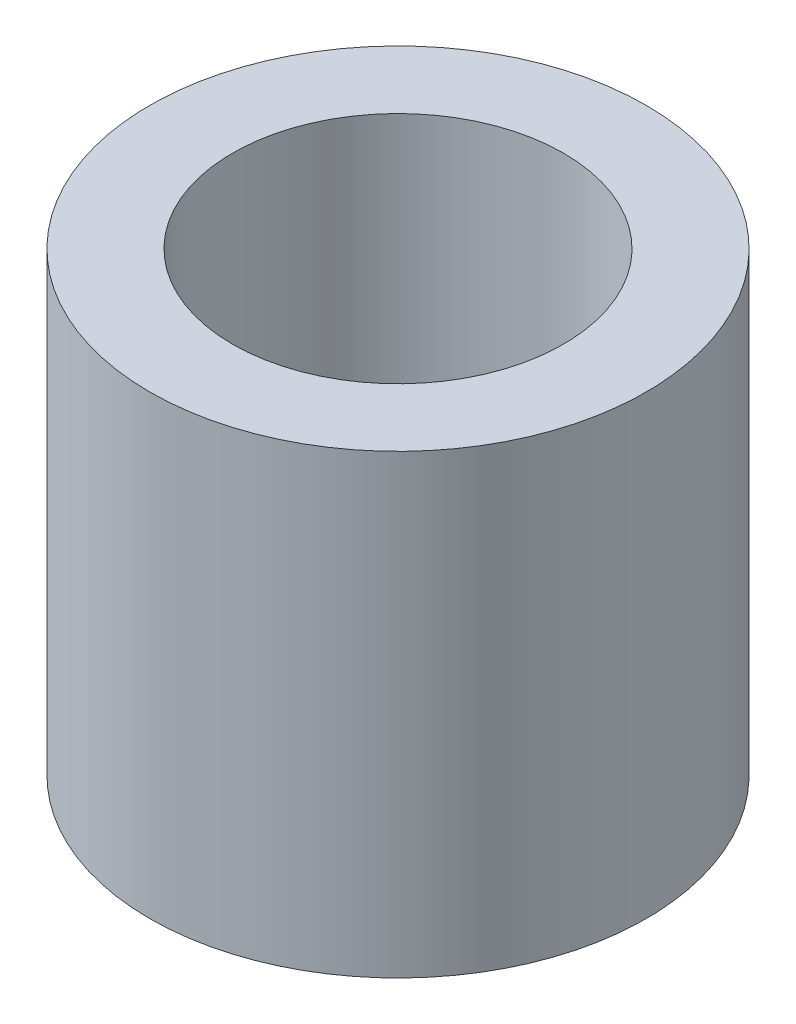
SolidWorks part; units mm, degrees
material "PET"
ref_plane "Front Plane" through (0, 0, 0) normal (0, 0, 1) x (1, 0, 0)
ref_plane "Top Plane" through (0, 0, 0) normal (0, 1, 0) x (1, 0, 0)
ref_plane "Right Plane" through (0, 0, 0) normal (1, 0, 0) x (0, 0, -1)
sketch "Sketch1" plane through (0, 0, 0) normal (0, 1, 0) x (1, 0, 0)
  circle A0 centre (0, 0) radius 1.5875
  circle A1 centre (0, 0) radius 2.3813
  dimension "D1" = 3.175
  dimension "D2" = 4.7625
extrude "Boss-Extrude1" add sketch "Sketch1" along normal blind 4.375
